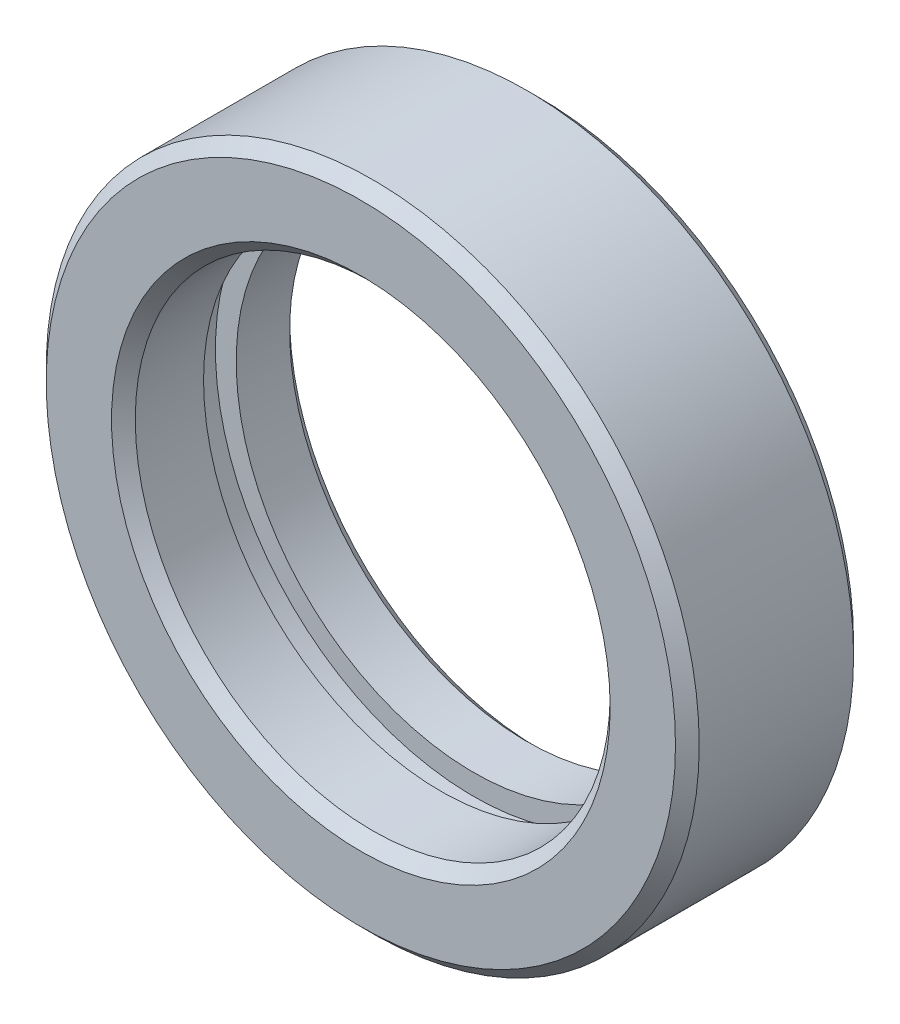
SolidWorks part; units mm, degrees
ref_plane "Front Plane" through (0, 0, 0) normal (0, 0, 1) x (1, 0, 0)
ref_plane "Top Plane" through (0, 0, 0) normal (0, 1, 0) x (1, 0, 0)
ref_plane "Right Plane" through (0, 0, 0) normal (1, 0, 0) x (0, 0, -1)
sketch "Sketch1" plane through (0, 0, 0) normal (0, 0, 1) x (1, 0, 0)
  circle A0 centre (0, 0) radius 55
  circle A1 centre (0, 0) radius 40
  dimension "D1" = 80
  dimension "D2" = 110
extrude "Boss-Extrude1" add sketch "Sketch1" along normal mid plane 30
chamfer "Chamfer1" distance 2 angle 45 4 edges at (40, 0, -15) (40, 0, 15) (55, 0, -15) (55, 0, 15)
sketch "Sketch2" plane through (0, 0, 0) normal (0, 1, 0) x (1, 0, 0)
  line L0 (0, 0) -> (0, 24.6629) construction
  line L1 (42, 15) -> (-42, 15) construction
  line L2 (-35.5858, 4) -> (-43.5, 4)
  line L3 (-35.5858, 4) -> (-35.5858, -1.5)
  line L4 (-35.5858, -1.5) -> (-43.5, -1.5)
  line L5 (-43.5, 4) -> (-43.5, -1.5)
  dimension "D1" = 87
  dimension "D2" = 5.5
  dimension "D3" = 11
revolve "Cut-Revolve1" cut sketch "Sketch2" angle 360 about L0
